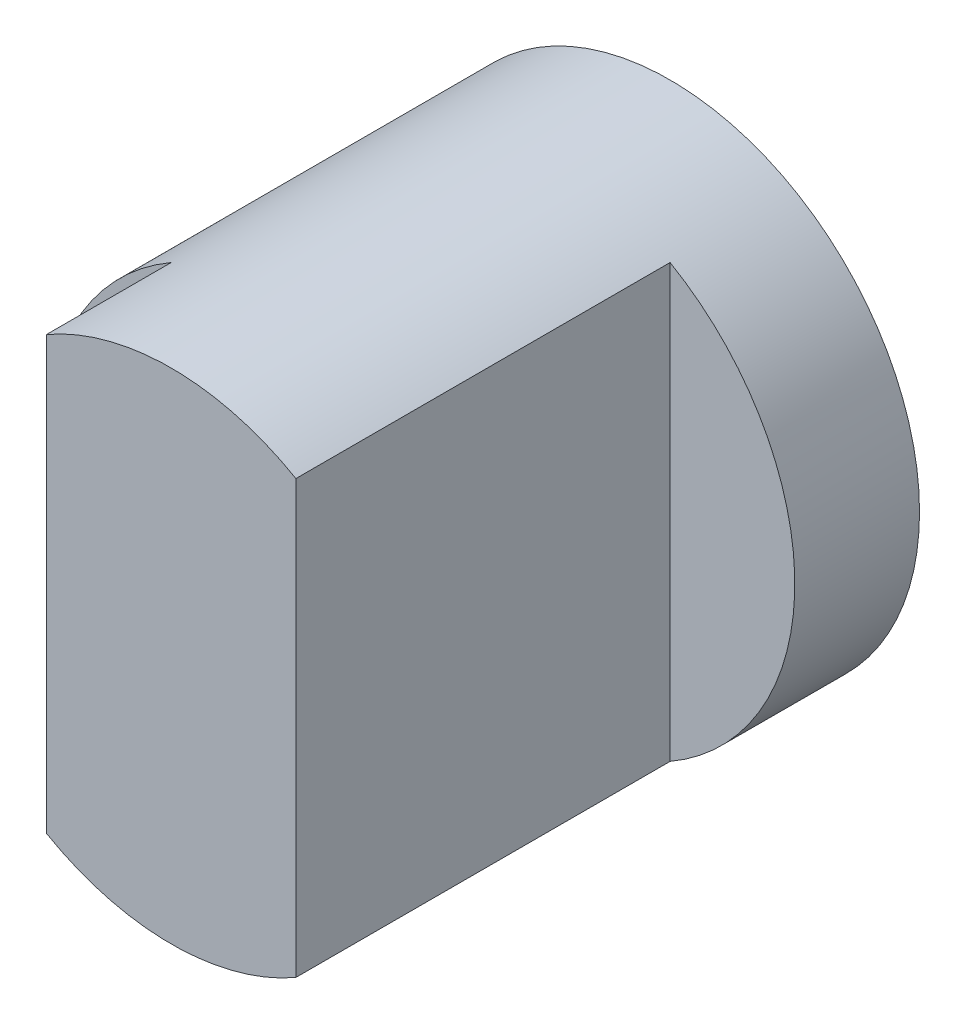
SolidWorks part; units mm, degrees
ref_plane "Front" through (0, 0, 0) normal (0, 0, 1) x (1, 0, 0)
ref_plane "Top" through (0, 0, 0) normal (0, 1, 0) x (1, 0, 0)
ref_plane "Right" through (0, 0, 0) normal (1, 0, 0) x (0, 0, -1)
sketch "Sketch1" plane through (0, 0, 0) normal (0, 0, 1) x (1, 0, 0)
  circle A0 centre (0, 0) radius 2
  dimension "D1" = 4
extrude "Boss-Extrude1" add sketch "Sketch1" along normal blind 4
sketch "Sketch2" plane through (0, 0, 0) normal (0, 1, 0) x (1, 0, 0)
  line L1 (2, -4) -> (1, -4)
  line L2 (2, -4) -> (2, -1)
  line L3 (2, -1) -> (1, -1)
  line L4 (1, -4) -> (1, -1)
  line L5 (-2, -4) -> (-1, -4)
  line L6 (-2, -4) -> (-2, -3)
  line L7 (-2, -3) -> (-1, -3)
  line L8 (-1, -4) -> (-1, -3)
  dimension "D1" = 1
  dimension "D2" = 1
  dimension "D3" = 1
  dimension "D4" = 3
extrude "Cut-Extrude1" cut sketch "Sketch2" against normal mid plane 10
